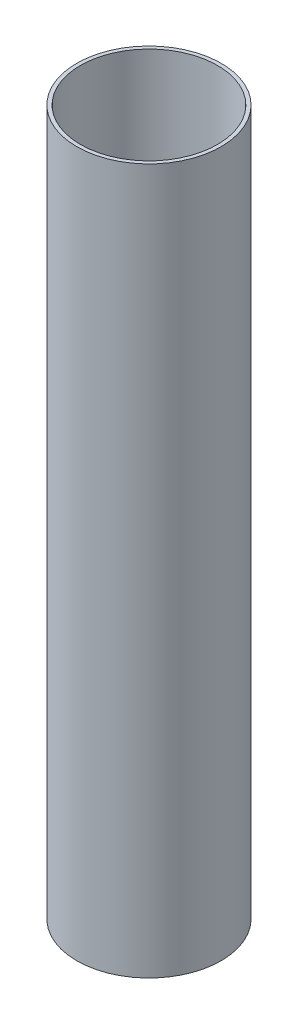
SolidWorks part; units mm, degrees
material "PVC Rigid"
ref_plane "Front Plane" through (0, 0, 0) normal (0, 0, 1) x (1, 0, 0)
ref_plane "Top Plane" through (0, 0, 0) normal (0, 1, 0) x (1, 0, 0)
ref_plane "Right Plane" through (0, 0, 0) normal (1, 0, 0) x (0, 0, -1)
sketch "Sketch1" plane through (0, 0, 0) normal (0, 1, 0) x (1, 0, 0)
  circle A0 centre (0, 0) radius 93.6625
  circle A1 centre (0, 0) radius 88.9
  dimension "D1" = 187.325
  dimension "D2" = 177.8
extrude "Boss-Extrude1" add sketch "Sketch1" along normal mid plane 914.4
